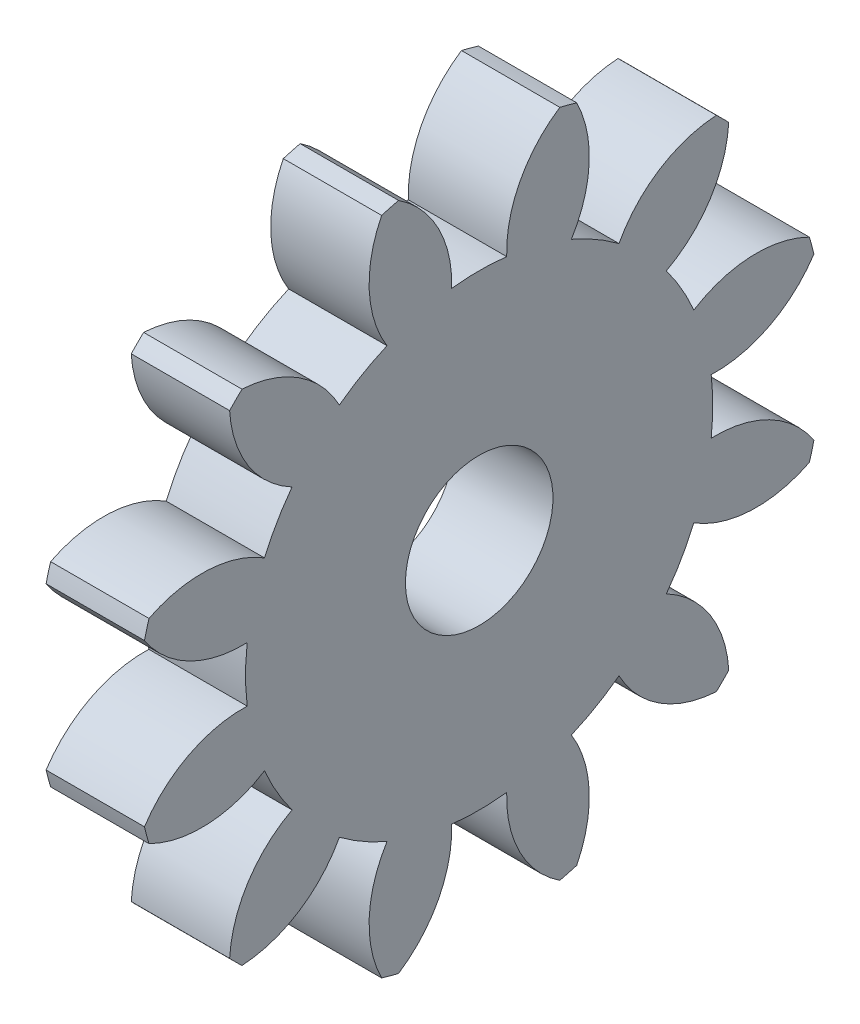
SolidWorks part; units mm, degrees
ref_plane "Plane1" through (0, 0, 0) normal (0, 0, 1) x (1, 0, 0)
ref_plane "Plane2" through (0, 0, 0) normal (0, 1, 0) x (1, 0, 0)
ref_plane "Plane3" through (0, 0, 0) normal (1, 0, 0) x (0, 0, -1)
sketch "HoldingSke" plane through (0, 0, 0) normal (0, 1, 0) x (1, 0, 0)
  line L0 (0, 0) -> (98.996, -22.855)
  line L1 (-15, 0) -> (100, 0) construction
  line L2 (0, 0) -> (-2.1039, 2.3779)
  line L3 (0, 0) -> (-11.863, 4.5341)
  line L4 (0, 0) -> (8.4473, 1.7955)
  line L5 (0, 0) -> (-23.7986, -8.8762)
  line L6 (0, 0) -> (-10.5278, -7.1032)
  line L7 (-2.1039, 2.3779) -> (3.3635, 27.1825)
  line L8 (-76.2, 54.61) -> (-54.61, 54.61)
  line L9 (-71.009, 38.7566) -> (-53.1078, 45.2721)
  line L10 (-76.2, 71.12) -> (104.1128, 71.12)
  line L11 (0, 0) -> (-12.7, 0)
  line L12 (-76.2, 101.6) -> (-75.9714, 101.6)
  line L13 (24.9733, 27.94) -> (52.9518, 28.4284)
  line L14 (24.9733, 27.94) -> (24.9746, 27.94)
  line L15 (24.9733, 27.94) -> (100.4006, 29.5858)
  circle A0 centre (0, 0) radius 9.525
  circle A1 centre (0, 0) radius 12.7
  circle A2 centre (0, 0) radius 12.7
  circle A3 centre (0, 0) radius 9.525
  dimension "Hub_dia" = 25.4
  dimension "Ap" = 20
  dimension "H" = 19.05
  dimension "Pitch_radius" = 180.3128
  dimension "Addendum_fac" = 1
  dimension "Dedendum_fac" = 1.25
  dimension "Clearance_fac" = 0.25
  dimension "Dedendum_add" = 0.0013
sketch "BasProSke" plane through (0, 0, 0) normal (0, 1, 0) x (1, 0, 0)
  line L0 (-10, 0) -> (60, 0) construction
  line L1 (0, 0) -> (0, 44.45)
  line L2 (0, 0) -> (12.7, 0)
  line L3 (12.7, 0) -> (12.7, 44.45)
  line L4 (12.7, 44.45) -> (0, 44.45)
revolve "Base-Revolve" add sketch "BasProSke" angle 360 about L0
sketch "TooCutSke" plane through (0, 0, 0) normal (1, 0, 0) x (0, 0, -1)
  line L1 (0, 0) -> (0, 107) construction
  line L2 (0, 0) -> (-5.3725, 37.7193) construction
  line L3 (0, 0) -> (-19.5794, 73.0714) construction
  line L4 (-5.3725, 37.7193) -> (-9.7897, 36.5357) construction
  arc A0 (3.5522, 29.9513) -> (-3.5522, 29.9513) centre (0, 0) ccw
  arc A1 (10.4397, 43.2328) -> (-10.4397, 43.2328) centre (0, 0) ccw
  circle A2 centre (0, 0) radius 38.1 construction
  circle A3 centre (0, 0) radius 35.8023 construction
  arc A4 (-3.5522, 29.9513) -> (-10.4397, 43.2328) centre (-18.7831, 30.4795) ccw
  arc A5 (10.4397, 43.2328) -> (3.5522, 29.9513) centre (18.7831, 30.4795) ccw
extrude "ToothCut" cut sketch "TooCutSke" along normal through all
fillet "Breaks" [suppressed] radius 0.127
fillet "RootFillets" [suppressed] radius 1.5888
pattern_circular "TeethCuts" count 12 every 30 about axis through (-10, 0, 0) along (1, 0, 0) of "ToothCut", "RootFillets", "Breaks"
sketch "HubNeaOneSke" plane through (0, 0, 0) normal (-1, 0, 0) x (0, 0, 1)
  circle A0 centre (0, 0) radius 12.7
extrude "HubNearOne" [suppressed] add sketch "HubNeaOneSke" along normal blind 12.7001
sketch "HubNeaBotSke" plane through (0, 0, 0) normal (-1, 0, 0) x (0, 0, 1)
  circle A0 centre (0, 0) radius 12.7
extrude "HubNearBoth" [suppressed] add sketch "HubNeaBotSke" along normal blind 6.35
ref_plane "FarPln" through (12.7, 0, 0) normal (1, 0, 0) x (0, 0, -1)
sketch "HubFarSke" plane through (12.7, 0, 0) normal (1, 0, 0) x (0, 0, -1)
  circle A0 centre (0, 0) radius 12.7
extrude "HubFar" [suppressed] add sketch "HubFarSke" along normal blind 6.35
sketch "BorSke" plane through (0, 0, 0) normal (1, 0, 0) x (0, 0, -1)
  circle A0 centre (0, 0) radius 9.525
extrude "Bore" cut sketch "BorSke" along normal mid plane 50.8001
sketch "KeySke" plane through (0, 0, 0) normal (1, 0, 0) x (0, 0, -1)
  line L0 (-3.175, 0) -> (-3.175, 12.065)
  line L1 (-3.175, 12.065) -> (3.175, 12.065)
  line L2 (3.175, 12.065) -> (3.175, 0)
  line L3 (0, 0) -> (0, 34) construction
  line L4 (-3.175, 0) -> (3.175, 0)
  dimension "Width" = 6.35
extrude "Keyway" [suppressed] cut sketch "KeySke" along normal mid plane 50.8001
pattern_circular "Keyway2" [suppressed] count 2 every 90 about axis through (-10, 0, 0) along (1, 0, 0)
equation "' \"Pitch@HoldingSke\" = 4"
equation "' \"Num_teeth@HoldingSke\" = 12"
equation "' \"Ap@HoldingSke\" =  20"
equation "' \"Ap@HoldingSke\" = 20"
equation "' \"Width@HoldingSke\" = 0.5"
equation "' \"Hub_dia@HoldingSke\"= 1"
equation "' \"Hub_dia@HoldingSke\" = 1"
equation "' \"Overall_len@HoldingSke\" = 1.0"
equation "' \"Bore@HoldingSke\" = 0.75"
equation "' \"T_dim@HoldingSke\" = 0.85"
equation "' \"Width@KeySke\" = 0.25"
equation "' \"Show_teeth@HoldingSke\" = 13"
equation "' \"Backlash@HoldingSke\" = 0.009"
equation "' \"Addendum_fac@HoldingSke\" = 1.0"
equation "' \"Dedendum_fac@HoldingSke\" = 1.25"
equation "' \"Dedendum_add@HoldingSke\" = 0.00005"
equation "' \"Clearance_fac@HoldingSke\" = 0.25"
equation "' \"Pitch@HoldingSke\" = 0.5"
equation "' \"Num_teeth@HoldingSke\" = 23"
equation "' \"Show_teeth@HoldingSke\" = 23"
equation "' \"Backlash@HoldingSke\" = 0.0375"
equation "\"Overcut_dia@TooCutSke\" = (\"Num_teeth@HoldingSke\" + 2 * \"Addendum_fac@HoldingSke\") / \"Pitch@HoldingSke\" + 0.002"
equation "\"Pitch_dia@TooCutSke\" = \"Num_teeth@HoldingSke\" / \"Pitch@HoldingSke\""
equation "\"Base_dia@TooCutSke\" = \"Num_teeth@HoldingSke\" / \"Pitch@HoldingSke\" * cos((\"Ap@HoldingSke\"  * 3.14159265 / 180))"
equation "\"Root_dia@TooCutSke\" = (\"Num_teeth@HoldingSke\" + 2) / \"Pitch@HoldingSke\" - 2 * (\"Addendum_fac@HoldingSke\" + \"Dedendum_fac@HoldingSke\") / \"Pitch@HoldingSke\" - \"Dedendum_add@HoldingSke\" * 2"
equation "\"Half_ang@TooCutSke\" = 180 / \"Num_teeth@HoldingSke\""
equation "\"Half_CT@TooCutSke\" = \"Num_teeth@HoldingSke\" / \"Pitch@HoldingSke\" * sin((3.14159265 / 2 / \"Num_teeth@HoldingSke\")) / 2 - 7 * \"Backlash@HoldingSke\" / 4"
equation "\"Flank_rad@TooCutSke\" = \"Num_teeth@HoldingSke\" / \"Pitch@HoldingSke\" / 5"
equation "\"Radius@RootFillets\" = \"Clearance_fac@HoldingSke\" / \"Pitch@HoldingSke\" + \"Dedendum_add@HoldingSke\""
equation "\"Break_rad@Breaks\" = 0.02 / \"Pitch@HoldingSke\""
equation "\"Thickness@HoldingSke\" = \"Width@HoldingSke\""
equation "\"OAL@HoldingSke\" = \"Thickness@HoldingSke\""
equation "\"MHD@HoldingSke\" = (\"Num_teeth@HoldingSke\" + 2) / \"Pitch@HoldingSke\" - 2 * (\"Addendum_fac@HoldingSke\" + \"Dedendum_fac@HoldingSke\")  / \"Pitch@HoldingSke\" - \"Dedendum_add@HoldingSke\" * 2"
equation "\"MBD@HoldingSke\" = (\"Num_teeth@HoldingSke\" + 2) / \"Pitch@HoldingSke\" - 2 * (\"Addendum_fac@HoldingSke\" + \"Dedendum_fac@HoldingSke\")  / \"Pitch@HoldingSke\" - \"Dedendum_add@HoldingSke\" * 2 - 0.002"
equation "\"MHD@HoldingSke\" = ((sgn( \"MHD@HoldingSke\" - \"Hub_dia@HoldingSke\" )-1)*( \"MHD@HoldingSke\" - \"Hub_dia@HoldingSke\" ))/-2+ \"Hub_dia@HoldingSke\""
equation "\"MBD@HoldingSke\" = ((sgn( \"MBD@HoldingSke\" - \"Bore@HoldingSke\" )-1)*( \"MBD@HoldingSke\" - \"Bore@HoldingSke\" ))/-2+ \"Bore@HoldingSke\""
equation "\"OAL@HoldingSke\" = ((sgn( \"OAL@HoldingSke\" - \"Overall_len@HoldingSke\" )+1)*( \"OAL@HoldingSke\" - \"Overall_len@HoldingSke\" ))/2 + \"Overall_len@HoldingSke\" + 0.000002"
equation "\"Num_teeth@TeethCuts\" = int( \"Show_teeth@HoldingSke\" ) + 1"
equation "\"Num_teeth@TeethCuts\" = ((sgn( \"Num_teeth@TeethCuts\" - \"Num_teeth@HoldingSke\" )-1)*( \"Num_teeth@TeethCuts\" - \"Num_teeth@HoldingSke\" ))/-2+ \"Num_teeth@HoldingSke\""
equation "\"Num_teeth@TeethCuts\" = ((sgn( \"Num_teeth@TeethCuts\" - 2.0)+1)*( \"Num_teeth@TeethCuts\" - 2.0))/2 +2.0"
equation "\"Angle@TeethCuts\" = 360.0 / \"Num_teeth@HoldingSke\""
equation "\"Diameter@BasProSke\" = (\"Num_teeth@HoldingSke\" + 2 * \"Addendum_fac@HoldingSke\") / \"Pitch@HoldingSke\""
equation "\"Thickness@BasProSke\"  = \"Thickness@HoldingSke\""
equation "' \"Fillet_rad@BasProSke\" =  \"Thickness@HoldingSke\" * 0.05"
equation "' \"Fillet_rad@BasProSke\" = \"Thickness@HoldingSke\" * 0.05"
equation "\"MHD@HoldingSke\" = ((sgn( \"MHD@HoldingSke\" - \"Root_dia@TooCutSke\" )-1)*( \"MHD@HoldingSke\" - \"Root_dia@TooCutSke\" ))/-2+ \"Root_dia@TooCutSke\""
equation "\"Diameter@HubNeaOneSke\" = \"MHD@HoldingSke\""
equation "\"Length@HubNearOne\" = \"OAL@HoldingSke\" - \"Thickness@BasProSke\""
equation "\"Diameter@HubNeaBotSke\" = \"MHD@HoldingSke\""
equation "\"Length@HubNearBoth\" = ( \"OAL@HoldingSke\" - \"Thickness@BasProSke\" ) / 2.0"
equation "\"Thickness@FarPln\" = \"Thickness@BasProSke\""
equation "\"Diameter@HubFarSke\" = \"MHD@HoldingSke\""
equation "\"Length@HubFar\" = ( \"OAL@HoldingSke\" - \"Thickness@BasProSke\" ) / 2.0"
equation "\"Diameter@BorSke\" = \"MBD@HoldingSke\""
equation "\"D1@Bore\" = \"OAL@HoldingSke\" * 2.0"
equation "\"D1@Keyway\" = \"OAL@HoldingSke\" * 2.0"
equation "\"Offset@KeySke\" = \"T_dim@HoldingSke\" - \"MBD@HoldingSke\" / 2.0"
